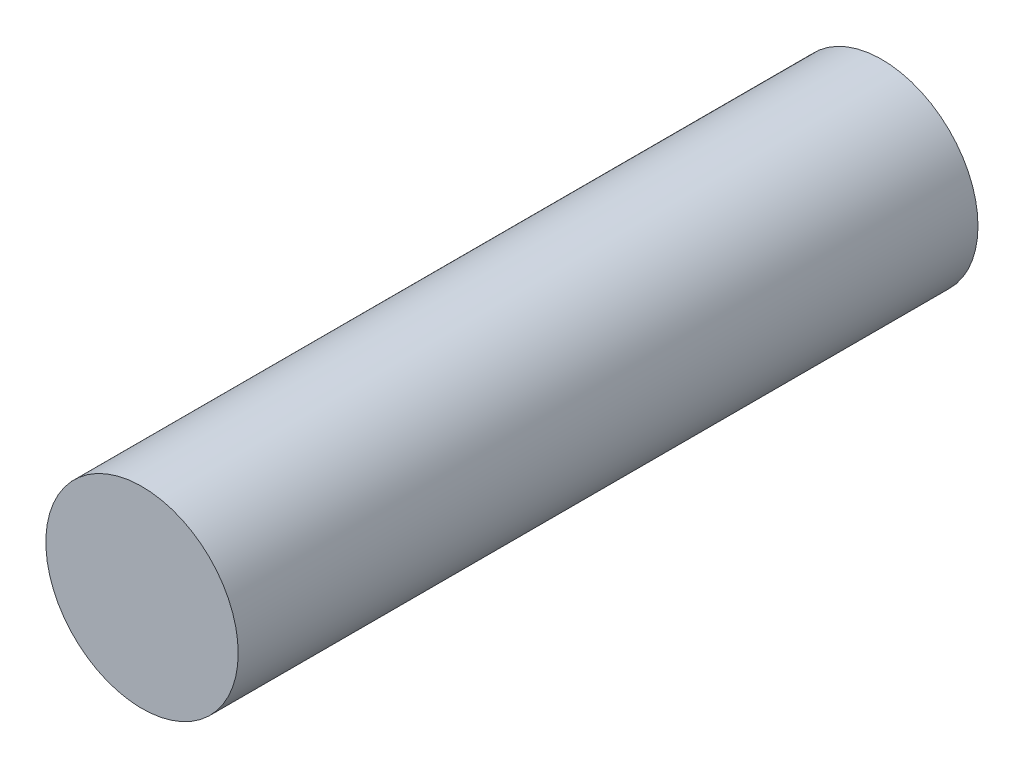
SolidWorks part; units mm, degrees
ref_plane "Front Plane" through (0, 0, 0) normal (0, 0, 1) x (1, 0, 0)
ref_plane "Top Plane" through (0, 0, 0) normal (0, 1, 0) x (1, 0, 0)
ref_plane "Right Plane" through (0, 0, 0) normal (1, 0, 0) x (0, 0, -1)
sketch "Sketch1" plane through (0, 0, 0) normal (0, 0, 1) x (1, 0, 0)
  circle A0 centre (0, 0) radius 0.65
  dimension "D1" = 1.3
extrude "Extrude1" add sketch "Sketch1" along normal blind 5
sketch "Sketch2" plane through (0, 0, 0) normal (0, 1, 0) x (1, 0, 0)
  line L0 (-0.65, 0) -> (-0.65, -5) construction
  line L1 (0.65, 0) -> (-0.65, 0) construction
  line L2 (0, -2.5) -> (0, -2.2717)
  line L3 (0, -2.5) -> (0.2283, -2.5)
  circle A0 centre (0, -2.5) radius 0.2283
  dimension "D1" = 0.65
  dimension "D2" = 2.5
